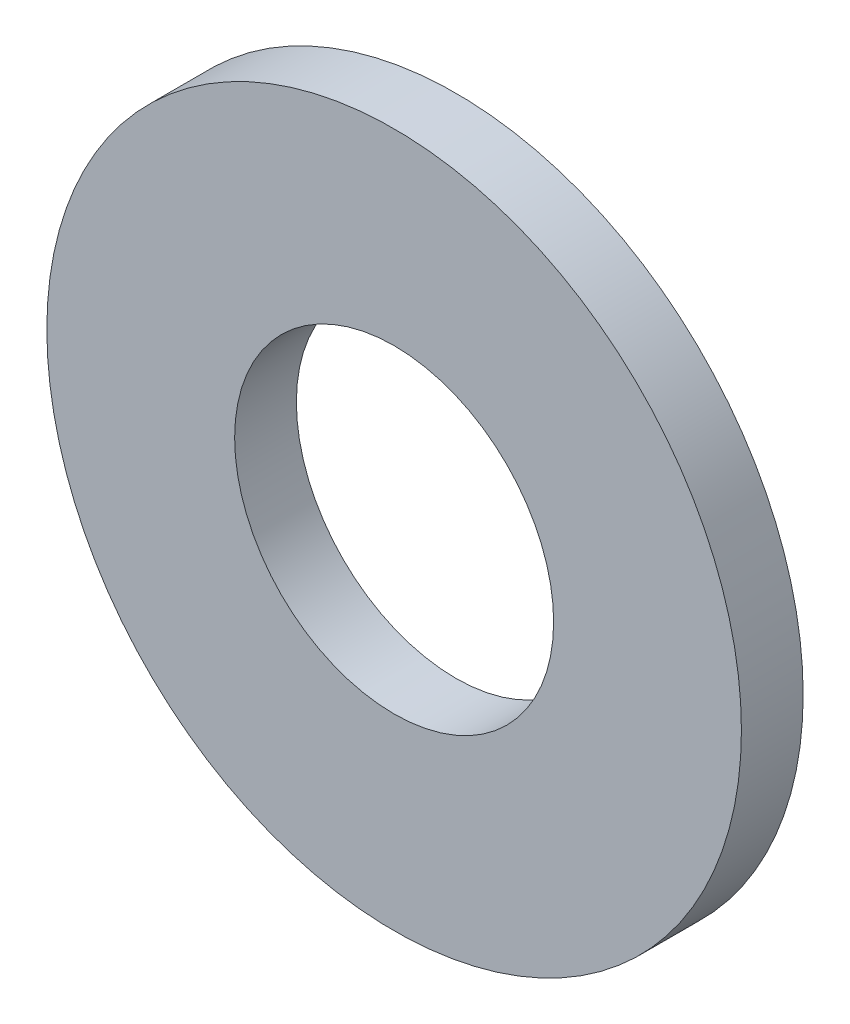
SolidWorks part; units mm, degrees
material "AISI Тип A2 Инструментальная сталь"
ref_plane "Front" through (0, 0, 0) normal (0, 0, 1) x (1, 0, 0)
ref_plane "Top" through (0, 0, 0) normal (0, 1, 0) x (1, 0, 0)
ref_plane "Right" through (0, 0, 0) normal (1, 0, 0) x (0, 0, -1)
sketch "Эскиз1" plane through (0, 0, 0) normal (0, 0, 1) x (1, 0, 0)
  circle A0 centre (0, 0) radius 3.375
  circle A1 centre (0, 0) radius 1.55
extrude "Бобышка-Вытянуть1" add sketch "Эскиз1" along normal blind 0.6
